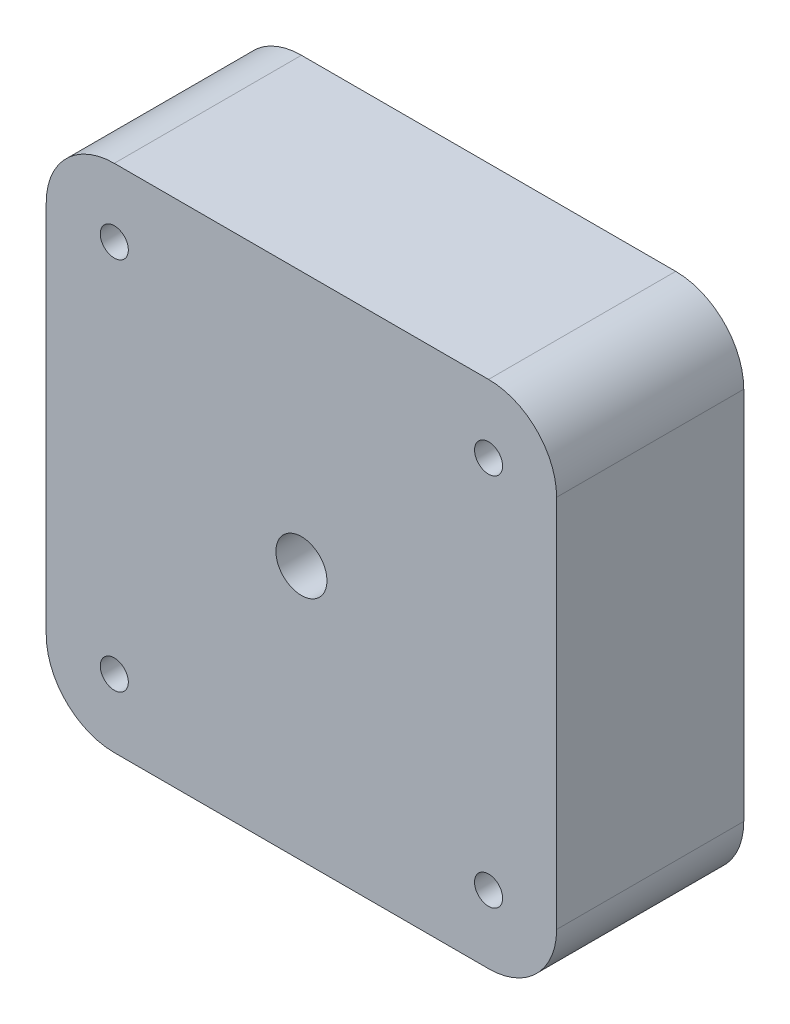
SolidWorks part; units mm, degrees
ref_plane "Front" through (0, 0, 0) normal (0, 0, 1) x (1, 0, 0)
ref_plane "Top" through (0, 0, 0) normal (0, 1, 0) x (1, 0, 0)
ref_plane "Right" through (0, 0, 0) normal (1, 0, 0) x (0, 0, -1)
sketch "Sketch1" plane through (0, 0, 0) normal (0, 0, 1) x (1, 0, 0)
  line L1 (-30, 30) -> (30, 30)
  line L2 (-30, 30) -> (-30, -30)
  line L3 (-30, -30) -> (30, -30)
  line L4 (30, 30) -> (30, -30)
  line L5 (0, -30) -> (0, 30) construction
  line L6 (-30, 0) -> (30, 0) construction
  point P0 (0, 0)
  dimension "D1" = 60
  dimension "D2" = 60
extrude "Boss-Extrude1" add sketch "Sketch1" along normal blind 22
sketch "Sketch2" plane through (0, 0, 0) normal (0, 0, -1) x (-1, 0, 0)
  circle A0 centre (0, 0) radius 3
  dimension "D1" = 6
extrude "Cut-Extrude1" cut sketch "Sketch2" against normal through all
chamfer "Chamfer1" distance 3 angle 45 1 edges at (-3, 0, 0)
fillet "Fillet1" radius 8 4 edges at (30, -30, 11) (-30, -30, 11) (30, 30, 11) (-30, 30, 11)
hole_wizard "M4x0.7 Tapped Hole1" positions "Sketch4" profile "Sketch3" tap size "M4x0.7" standard "ANSI Metric" end condition through all
sketch "Sketch4" plane through (0, 0, 0) normal (0, 0, -1) x (-1, 0, 0)
  point P0 (-22, 22)
  point P2 (22, 22)
  point P4 (22, -22)
  point P6 (-22, -22)
  dimension "D1" = 22
  dimension "D2" = 22
  dimension "D3" = 22
  dimension "D4" = 22
sketch "Sketch3" plane through (22, 22, 0) normal (1, 0, 0) x (0, 1, 0)
  line L0 (0, 0) -> (0, 22)
  line L1 (0, 22) -> (1.65, 22)
  line L2 (1.65, 22) -> (1.65, 0)
  line L5 (1.65, 0) -> (0, 0)
  line L11 (0, -6.35) -> (0, 107.95) construction
  dimension "Thru Tap Drill Dia." = 3.3
  dimension "Thru Tap Drill Depth" = 22
cosmetic thread "Hole Thread1" parameters "D2"=4
cosmetic thread "Hole Thread2" parameters "D2"=4
cosmetic thread "Hole Thread3" parameters "D2"=4
cosmetic thread "Hole Thread4" parameters "D2"=4
